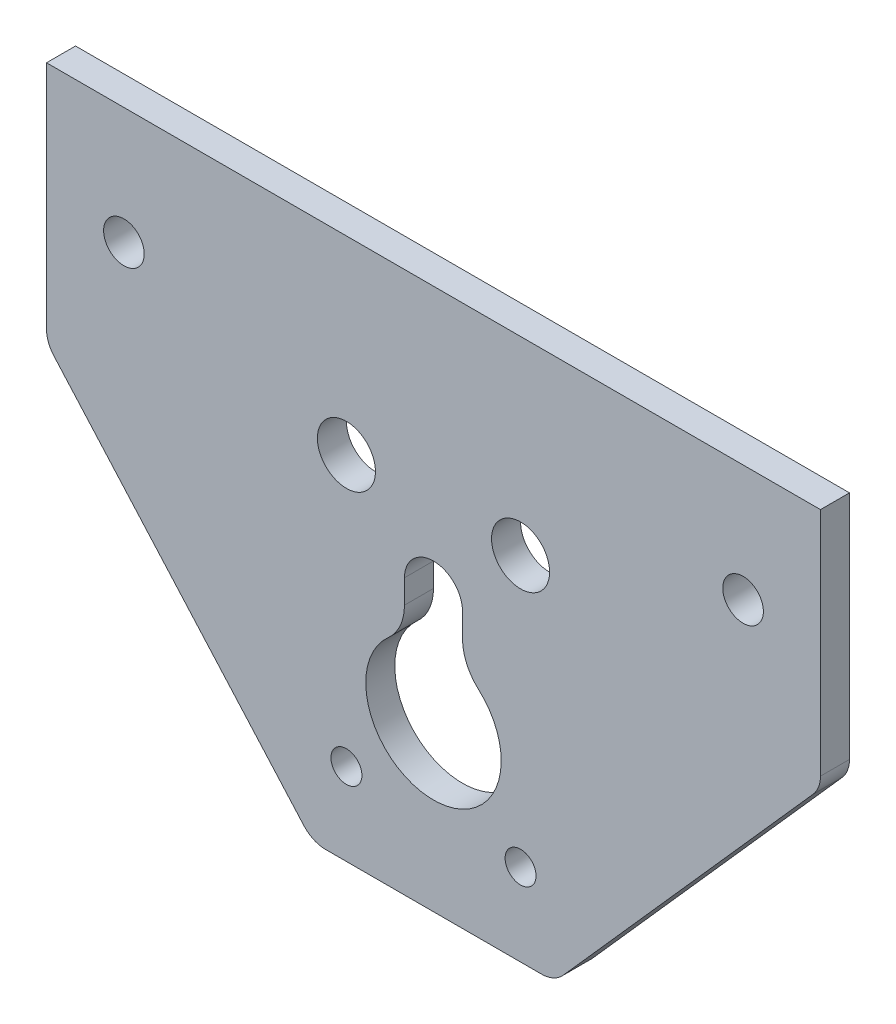
SolidWorks part; units mm, degrees
material "ABS PC"
ref_plane "Front Plane" through (0, 0, 0) normal (0, 0, 1) x (1, 0, 0)
ref_plane "Top Plane" through (0, 0, 0) normal (0, 1, 0) x (1, 0, 0)
ref_plane "Right Plane" through (0, 0, 0) normal (1, 0, 0) x (0, 0, -1)
sketch "Sketch2" plane through (0, 0, 0) normal (0, 0, 1) x (1, 0, 0)
  line L0 (0, 15.8362) -> (0, -20.7185) construction
  line L1 (-19.2162, 0) -> (23.097, 0) construction
  line L2 (-12.5, -17) -> (12.5, -17)
  line L3 (-40, 39) -> (40, 39)
  line L4 (-40, 39) -> (-40, 14)
  line L5 (-40, 14) -> (-12.5, -17)
  line L6 (40, 39) -> (40, 14)
  line L7 (40, 14) -> (12.5, -17)
  circle A0 centre (0, 0) radius 7
  circle A1 centre (-9, -8.5) radius 1.6
  circle A2 centre (9, -8.5) radius 1.6
  dimension "D1" = 14
  dimension "D2" = 3.2
  dimension "D3" = 3.2
  dimension "D4" = 9
  dimension "D5" = 9
  dimension "D6" = 8.5
  dimension "D7" = 8.5
  dimension "D8" = 80
  dimension "D9" = 56
  dimension "D10" = 25
  dimension "D11" = 17
  dimension "D12" = 25
extrude "Boss-Extrude1" add sketch "Sketch2" along normal blind 3
sketch "Sketch3" plane through (0, 0, 3) normal (0, 0, 1) x (1, 0, 0)
  line L0 (-41.3296, 26.93) -> (36.838, 26.93) construction
  line L1 (40, 39) -> (-40, 39) construction
  line L2 (40, 39) -> (-40, 39) construction
  line L3 (-40, 39) -> (-40, 14) construction
  line L4 (40, 14) -> (40, 39) construction
  line L5 (-40, 39) -> (-40, 14) construction
  line L6 (40, 14) -> (40, 39) construction
  line L7 (-31.999, 29.6401) -> (-31.999, 12.1307) construction
  line L8 (31.999, 28.3765) -> (31.999, 12.1307) construction
  circle A0 centre (31.999, 26.93) radius 2.1
  circle A1 centre (-31.999, 26.93) radius 2.1
  dimension "D1" = 12.07
  dimension "D4" = 4.2
  dimension "D2" = 8.001
  dimension "D3" = 8.001
extrude "Cut-Extrude1" cut sketch "Sketch3" against normal blind 10
fillet "Fillet1" radius 3 4 edges at (-40, 14, 1.5) (-12.5, -17, 1.5) (12.5, -17, 1.5) (40, 14, 1.5)
sketch "Sketch4" plane through (0, 0, 3) normal (0, 0, 1) x (1, 0, 0)
  line L0 (0, 0) -> (0, 42.0473) construction
  line L1 (-3, 11.4) -> (-3, 6.3246)
  line L2 (3, 11.4) -> (3, 6.3246)
  arc A0 (3, 11.4) -> (-3, 11.4) centre (0, 11.4) ccw
  circle A1 centre (9, 19.4) radius 3
  circle A2 centre (-9, 19.4) radius 3
  circle A3 centre (0, 0) radius 7 construction
  arc A4 (3, 6.3246) -> (-3, 6.3246) centre (0, 0) ccw
  dimension "D1" = 11.4
  dimension "D2" = 6
  dimension "D3" = 19.4
  dimension "D5" = 6
  dimension "D4" = 9
extrude "Cut-Extrude2" cut sketch "Sketch4" against normal blind 10
fillet "Fillet2" radius 5 2 edges at (3, 6.3246, 1.5) (-3, 6.3246, 1.5)
